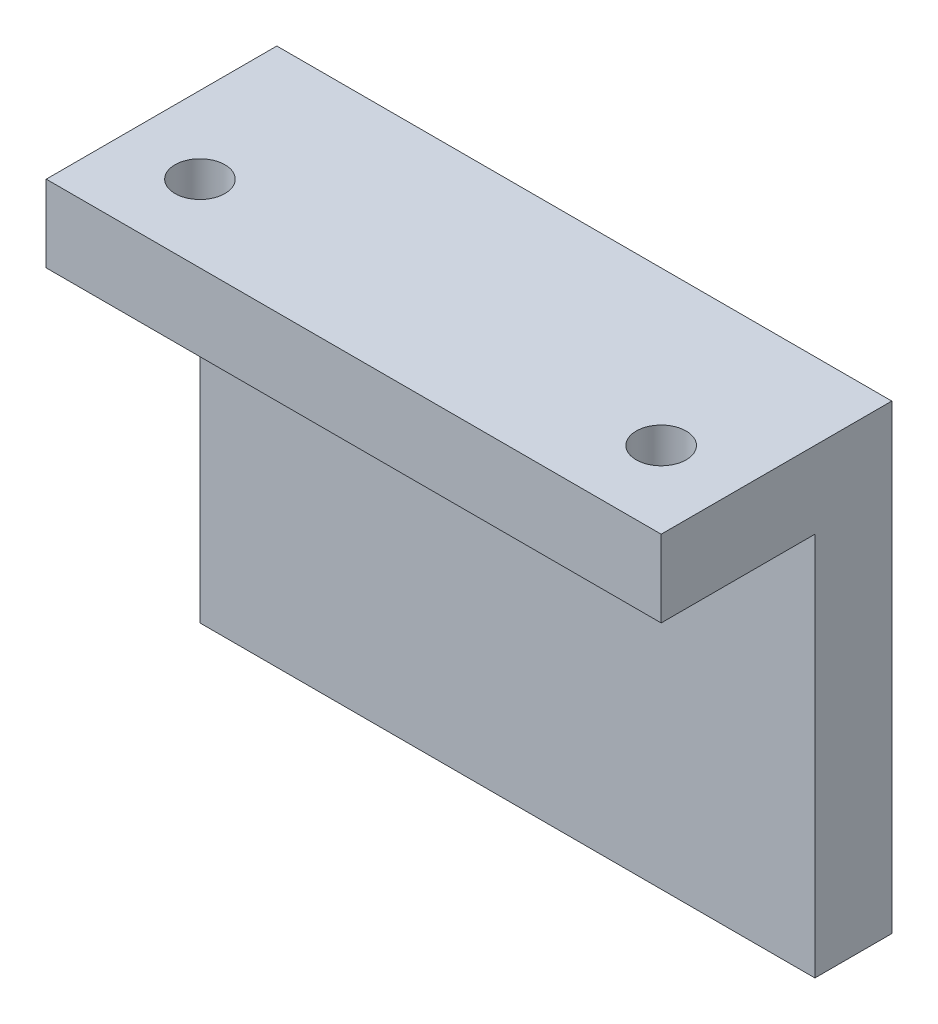
SolidWorks part; units mm, degrees
ref_plane "Plan de face" through (0, 0, 0) normal (0, 0, 1) x (1, 0, 0)
ref_plane "Plan de dessus" through (0, 0, 0) normal (0, 1, 0) x (1, 0, 0)
ref_plane "Plan de droite" through (0, 0, 0) normal (1, 0, 0) x (0, 0, -1)
sketch "Esquisse1" plane through (0, 0, 0) normal (0, 0, 1) x (1, 0, 0)
  line L1 (0, 0) -> (40, 0)
  line L2 (0, 0) -> (0, -30)
  line L3 (0, -30) -> (40, -30)
  line L4 (40, 0) -> (40, -30)
  dimension "D1" = 40
  dimension "D2" = 30
extrude "Boss.-Extru.1" add sketch "Esquisse1" along normal blind 5
sketch "Esquisse2" plane through (0, 0, 5) normal (0, 0, 1) x (1, 0, 0)
  line L0 (0, 0) -> (0, -30) construction
  line L1 (40, 0) -> (0, 0)
  line L2 (40, 0) -> (40, -5)
  line L3 (40, -5) -> (0, -5)
  line L4 (0, 0) -> (0, -5)
  dimension "D1" = 5
extrude "Boss.-Extru.2" add sketch "Esquisse2" along normal blind 10
sketch "Esquisse3" plane through (0, -5, 0) normal (0, -1, 0) x (1, 0, 0)
  line L0 (0, 15) -> (0, 5) construction
  circle A0 centre (5, 10) radius 1.625
  circle A1 centre (35, 10) radius 1.625
  point P6 (0, 10)
  dimension "D1" = 3.25
  dimension "D2" = 3.25
  dimension "D3" = 30
  dimension "D4" = 5
extrude "Enlèv. mat.-Extru.1" cut sketch "Esquisse3" against normal through all
sketch "Esquisse4" plane through (0, 0, 0) normal (0, 0, -1) x (-1, 0, 0)
  line L0 (-40, 0) -> (0, 0) construction
  line L1 (0, 0) -> (0, -30) construction
  circle A0 centre (-9.1, -20.9) radius 2.6
  dimension "D2" = 5.2
  dimension "D1" = 20.9
  dimension "D3" = 9.1
extrude "Enlèv. mat.-Extru.2" cut sketch "Esquisse4" against normal blind 4
